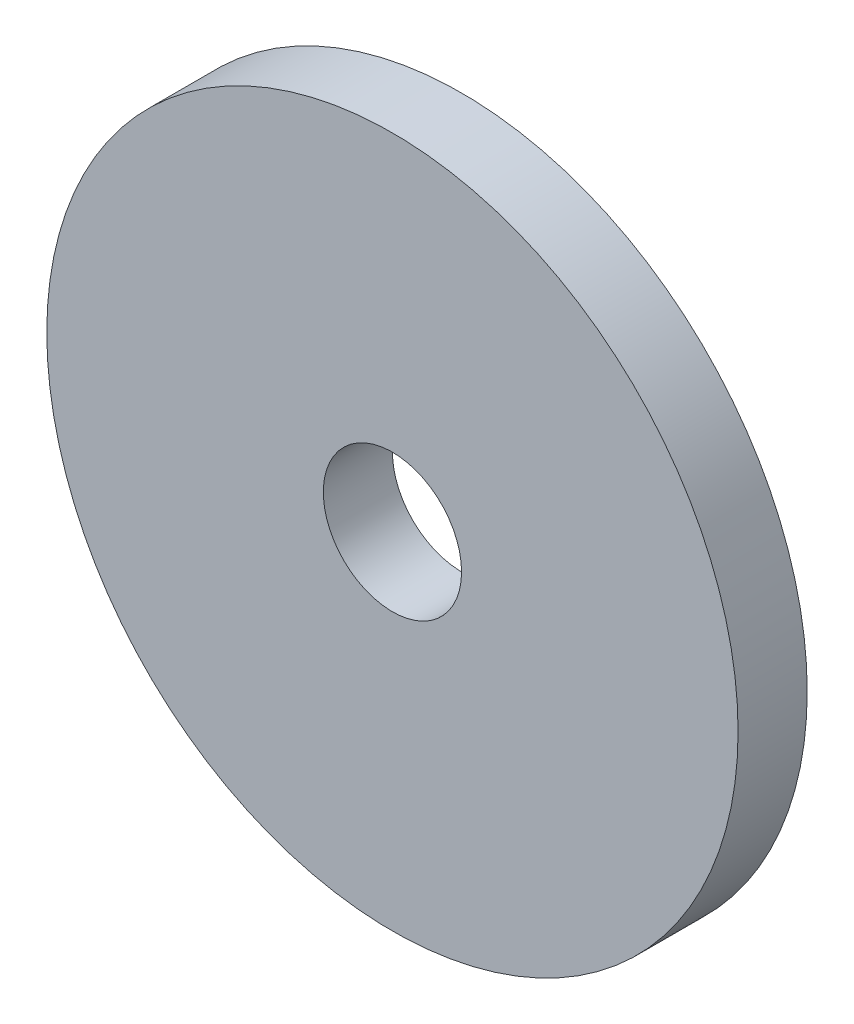
SolidWorks part; units mm, degrees
ref_plane "Front Plane" through (0, 0, 0) normal (0, 0, 1) x (1, 0, 0)
ref_plane "Top Plane" through (0, 0, 0) normal (0, 1, 0) x (1, 0, 0)
ref_plane "Right Plane" through (0, 0, 0) normal (1, 0, 0) x (0, 0, -1)
sketch "Sketch1" plane through (0, 0, 0) normal (0, 0, 1) x (1, 0, 0)
  circle A0 centre (-85, 68) radius 15
  circle A1 centre (-85, 68) radius 3
  dimension "D1" = 30
extrude "Boss-Extrude1" add sketch "Sketch1" along normal blind 3
